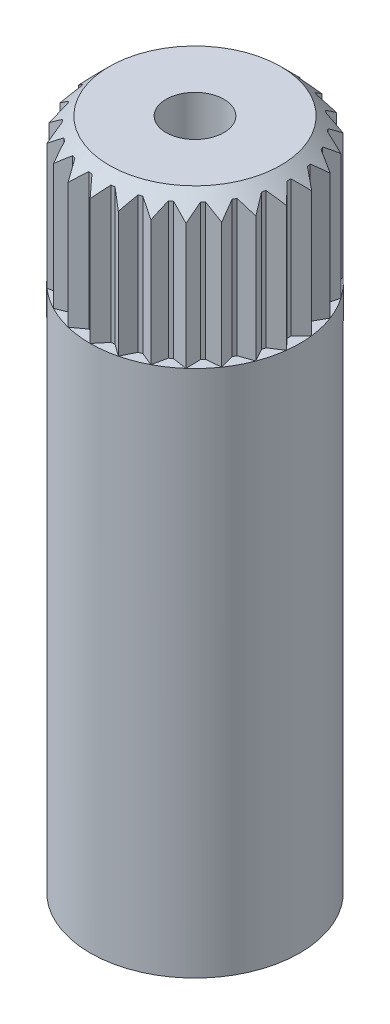
SolidWorks part; units mm, degrees
material "Polyethylene Cross-Linked"
ref_plane "Front Plane" through (0, 0, 0) normal (0, 0, 1) x (1, 0, 0)
ref_plane "Top Plane" through (0, 0, 0) normal (0, 1, 0) x (1, 0, 0)
ref_plane "Right Plane" through (0, 0, 0) normal (1, 0, 0) x (0, 0, -1)
sketch "Sketch12" plane through (0, 0, 0) normal (0, 1, 0) x (1, 0, 0)
  circle A0 centre (0, 0) radius 2.9
  dimension "D1" = 5.8
extrude "Boss-Extrude4" add sketch "Sketch12" along normal blind 14.6 separate body
sketch "Sketch13" plane through (0, 14.6, 0) normal (0, 1, 0) x (1, 0, 0)
  circle A2 centre (0, 0) radius 2.6
  circle A3 centre (0, 0) radius 2.9 construction
  dimension "D1" = 0.3
extrude "Boss-Extrude5" add sketch "Sketch13" along normal blind 4
sketch "Sketch14" plane through (0, 18.6, 0) normal (0, 1, 0) x (1, 0, 0)
  line L0 (0, 2.6) -> (0, 2.9) construction
  line L1 (0, 2.9) -> (-0.2629, 2.5867)
  line L2 (0, 2.9) -> (0.2629, 2.5867)
  line L3 (-0.2629, 2.5867) -> (0.2629, 2.5867) construction
  circle A0 centre (0, 0) radius 2.9 construction
  circle A1 centre (0, 0) radius 2.6
  arc A2 (0.2629, 2.5867) -> (-0.2629, 2.5867) centre (0, 0) ccw
  dimension "D2" = 80
  dimension "D3" = 0.5258
  dimension "D4" = 0.3
  dimension "D1" = 0
extrude "Boss-Extrude6" add sketch "Sketch14" against normal up to body (18.6 mm away)
pattern_circular "CirPattern1" count 26 over 360 about axis through (0, 0, 0) along (0, 1, 0) of "Boss-Extrude6"
sketch "Sketch15" plane through (0, 0, 0) normal (1, 0, 0) x (0, 0, -1)
  line L0 (2.9, 18.0697) -> (2.9, 18.6)
  line L1 (2.9, 14.6) -> (2.9, 18.6) construction
  line L2 (2.9, 18.6) -> (2.3697, 18.6)
  line L3 (2.1682, 18.6) -> (2.5678, 18.6) construction
  line L4 (2.3697, 18.6) -> (2.9, 18.0697)
  dimension "D1" = 45
  dimension "D2" = 0.75
revolve "Cut-Revolve1" cut sketch "Sketch15" angle 360 about axis through (0, 18.6, 0) along (0, -1, 0)
sketch "Sketch16" plane through (0, 18.6, 0) normal (0, 1, 0) x (1, 0, 0)
  circle A0 centre (0, 0) radius 0.8
  dimension "D1" = 1.6
extrude "Cut-Extrude1" cut sketch "Sketch16" against normal blind 4
ref_plane "Plane1" through (-0.3638, 14.6, -2.5744) normal (-0.9902, 0, 0.1399) x (0.1399, 0, 0.9902)
